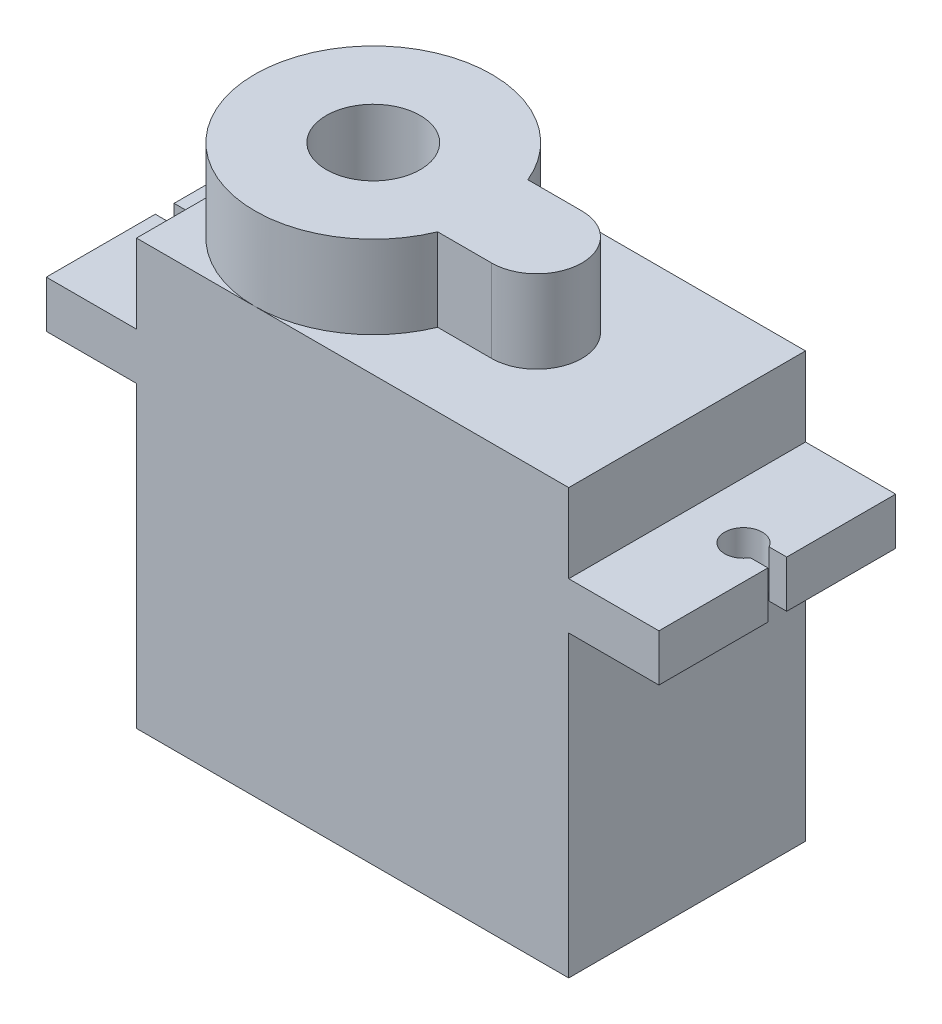
SolidWorks part; units mm, degrees
ref_plane "Alzado" through (0, 0, 0) normal (0, 0, 1) x (1, 0, 0)
ref_plane "Planta" through (0, 0, 0) normal (0, 1, 0) x (1, 0, 0)
ref_plane "Vista lateral" through (0, 0, 0) normal (1, 0, 0) x (0, 0, -1)
sketch "Croquis1" plane through (0, 0, 0) normal (0, 0, 1) x (1, 0, 0)
  line L0 (11.5, 0) -> (-11.5, 0)
  line L1 (-11.5, 0) -> (-11.5, 15.9)
  line L2 (-11.5, 15.9) -> (-16.3, 15.9)
  line L3 (-16.3, 15.9) -> (-16.3, 18.4)
  line L4 (-16.3, 18.4) -> (-11.5, 18.4)
  line L5 (-11.5, 18.4) -> (-11.5, 22.6)
  line L6 (-11.5, 22.6) -> (11.5, 22.6)
  line L8 (0, 35.0828) -> (0, -5.7212) construction
  line L9 (11.5, 0) -> (11.5, 15.9)
  line L10 (11.5, 15.9) -> (16.3, 15.9)
  line L11 (16.3, 15.9) -> (16.3, 18.4)
  line L12 (16.3, 18.4) -> (11.5, 18.4)
  line L13 (11.5, 18.4) -> (11.5, 22.6)
  dimension "D1" = 23
  dimension "D2" = 15.9
  dimension "D3" = 2.5
  dimension "D4" = 4.2
  dimension "D5" = 4.8
  dimension "D6" = 4.8
extrude "Saliente-Extruir1" add sketch "Croquis1" along normal blind 12.6 contours L1 L2 L3 L4 L5 L6 L13 L12 L11 L10 L9 L0
sketch "Croquis2" plane through (0, 18.4, 0) normal (0, 1, 0) x (1, 0, 0)
  line L0 (-16.3, -12.6) -> (-16.3, -6.8) construction
  line L1 (-16.3, -12.6) -> (-16.3, 0) construction
  line L2 (-16.3, -6.3) -> (16.3, -6.3) construction
  line L3 (16.3, -12.6) -> (16.3, 0) construction
  line L4 (-16.3, 0) -> (-16.3, -5.8) construction
  line L5 (-16.3, -6.8) -> (-15.366, -6.8)
  line L6 (-16.3, -5.8) -> (-15.366, -5.8)
  line L7 (0, 0) -> (0, -12.6) construction
  line L8 (-11.5, -12.6) -> (11.5, -12.6) construction
  line L9 (-16.3, -6.8) -> (-16.3, -5.8)
  line L10 (-15.366, -5.8) -> (-15.366, -6.8)
  line L11 (15.366, -5.8) -> (15.366, -6.8)
  line L12 (16.3, -5.8) -> (15.366, -5.8)
  line L13 (16.3, -6.8) -> (16.3, -5.8)
  line L14 (16.3, -6.8) -> (15.366, -6.8)
  line L15 (-13.5, -6.3) -> (-13.5, -4.3984) construction
  line L16 (-11.503, -6.3) -> (-11.5, -4.3984) construction
  line L17 (-11.5, -12.6) -> (-11.5, 0) construction
  line L18 (-11.5, -12.6) -> (-11.5, 0) construction
  line L19 (-16.3, -12.6) -> (-11.5, -12.6) construction
  circle A0 centre (-14.5, -6.3) radius 1
  circle A1 centre (14.5, -6.3) radius 1
  point P12 (-14.5, -6.3)
  dimension "D4" = 1
  dimension "D1" = 5.8
  dimension "D2" = 2
  dimension "D3" = 1.8
extrude "Cortar-Extruir2" cut sketch "Croquis2" against normal blind 2.5
sketch "Croquis4" plane through (0, 22.6, 0) normal (0, 1, 0) x (1, 0, 0)
  line L0 (-11.5, -6.3) -> (-5.2, -6.3) construction
  line L1 (-11.5, -12.6) -> (-11.5, 0) construction
  line L2 (-5.2, -6.3) -> (3.5, -6.3) construction
  line L4 (-1.3, -8.7) -> (3.5, -8.7)
  line L5 (-1.3, -8.7) -> (-1.3, -3.9)
  line L6 (-1.3, -3.9) -> (3.5, -3.9)
  line L7 (3.5, -8.7) -> (3.5, -3.9)
  line L8 (-1.3, -8.7) -> (3.5, -3.9) construction
  line L9 (-1.3, -3.9) -> (3.5, -8.7) construction
  circle A0 centre (-5.2, -6.3) radius 6.3
  circle A1 centre (3.5, -6.3) radius 2.4
  circle A2 centre (-5.2, -6.3) radius 2.5
  point P7 (1.1, -6.3)
  point P8 (1.1, -6.3)
  dimension "D2" = 12.6
  dimension "D4" = 4.8
  dimension "D5" = 5
  dimension "D1" = 6.3
  dimension "D3" = 8.7
extrude "Saliente-Extruir4" add sketch "Croquis4" along normal blind 4.4 contours A0 L4 L5 L6 A2 | L7 A1 | L7 A1 | A1 A0 L4 | A1 L6 A0 | L4 A0 L6 L5
